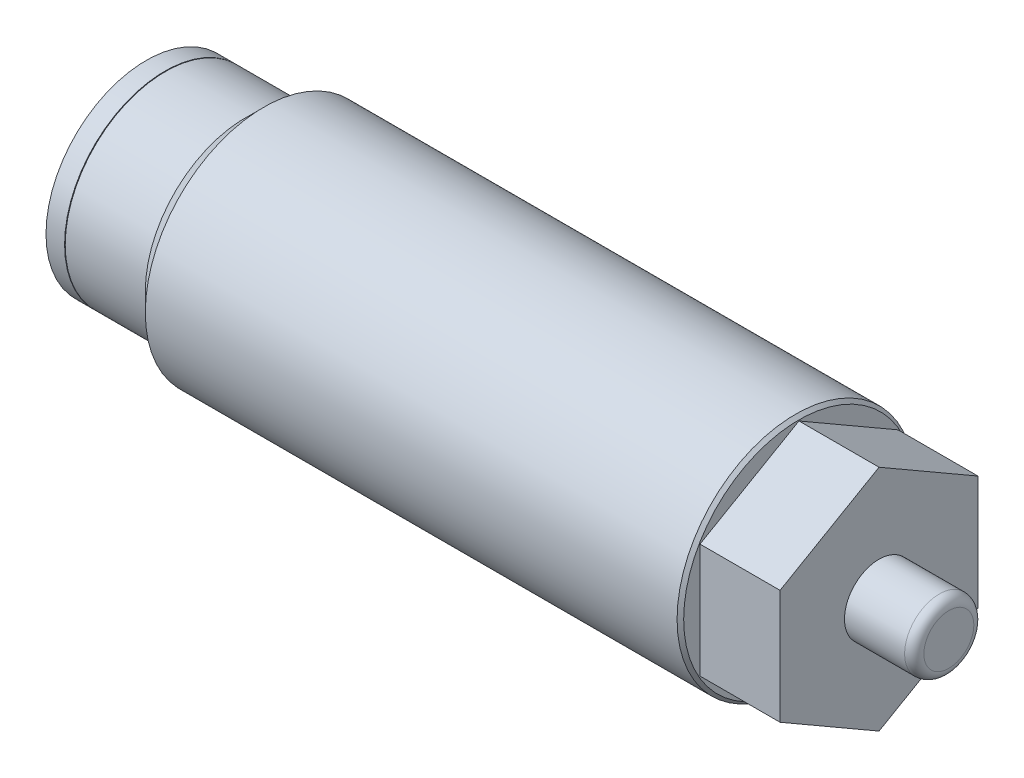
SolidWorks part; units mm, degrees
material "Alloy Steel"
ref_plane "Front Plane" through (0, 0, 0) normal (0, 0, 1) x (1, 0, 0)
ref_plane "Top Plane" through (0, 0, 0) normal (0, 1, 0) x (1, 0, 0)
ref_plane "Right Plane" through (0, 0, 0) normal (1, 0, 0) x (0, 0, -1)
sketch "Sketch11" plane through (0, 0, 0) normal (0, 0, 1) x (1, 0, 0)
  line L0 (-0.0254, 3.9751) -> (-0.762, 3.9751)
  line L1 (-0.762, 3.9751) -> (-0.762, 1.905)
  line L2 (-0.762, 1.905) -> (-0.0254, 1.905)
  line L3 (-0.0254, 1.905) -> (-0.0254, 3.9751)
  line L4 (-0.762, 0) -> (-0.0254, 0) construction
  dimension "D1" = 3.81
  dimension "D2" = 0.7366
  dimension "D3" = 7.9502
  dimension "D4" = 0.0254
revolve "Revolve5" add sketch "Sketch11" angle 360 about L4
ref_plane "Plane4" through (0, 0, 0) normal (0, 0, -1) x (-1, 0, 0)
sketch "Sketch12" plane through (0, 0, 0) normal (0, 0, -1) x (-1, 0, 0)
  line L0 (-25.1206, 4.7028) -> (-25.1206, 0)
  line L1 (0.0254, 3.9751) -> (0.0254, -3.9751) construction
  line L2 (0, 0) -> (0, 3.9751)
  line L3 (0, 3.9751) -> (-3.175, 3.9751)
  line L4 (-3.175, 3.9751) -> (-3.9027, 4.7028)
  line L5 (-3.9027, 4.7028) -> (-25.1206, 4.7028)
  line L6 (-30.6025, 0) -> (0, 0) construction
  line L7 (-25.1206, 0) -> (0, 0)
  dimension "D1" = 9.4056
  dimension "D2" = 0.0254
  dimension "D3" = 7.9502
  dimension "D4" = 45
  dimension "D5" = 3.175
  dimension "D6" = 25.1206
revolve "Revolve6" add sketch "Sketch12" angle 360 about L6
sketch "Sketch13" plane through (25.1206, 0, 0) normal (1, 0, 0) x (0, 0, -1)
  line L7 (3.9243, 2.2657) -> (0, 4.5314)
  line L8 (0, 4.5314) -> (-3.9243, 2.2657)
  line L9 (-3.9243, 2.2657) -> (-3.9243, -2.2657)
  line L10 (-3.9243, -2.2657) -> (0, -4.5314)
  line L11 (0, -4.5314) -> (3.9243, -2.2657)
  line L12 (3.9243, -2.2657) -> (3.9243, 2.2657)
  circle A0 centre (0, 0) radius 3.9243 construction
  dimension "D1" = 7.8486
extrude "Extrude3" add sketch "Sketch13" along normal blind 3.175
ref_plane "Plane5" through (0, 0, 0) normal (0, 0, 1) x (1, 0, 0)
sketch "Sketch14" plane through (0, 0, 0) normal (0, 0, 1) x (1, 0, 0)
  line L0 (28.2956, 1.3716) -> (28.2956, 0)
  line L1 (28.2956, 2.2657) -> (28.2956, -2.2657) construction
  line L2 (31.0642, 0) -> (31.0642, 1.3716)
  line L3 (31.0642, 1.3716) -> (28.2956, 1.3716)
  line L4 (28.2956, 0) -> (32.4342, 0) construction
  line L5 (28.2956, 0) -> (31.0642, 0)
  dimension "D1" = 2.7432
  dimension "D2" = 31.0642
revolve "Revolve7" add sketch "Sketch14" angle 360 about L4
hole_wizard "Hole3" positions "Sketch16" profile "Sketch15" legacy
sketch "Sketch16" plane through (0, 0, 0) normal (-1, 0, 0) x (0, 0, 1)
  point P0 (0, 0)
sketch "Sketch15" plane through (0, 0, 0) normal (0, 1, 0) x (0, 0, 1)
  line L0 (0, 0) -> (0, 0.254)
  line L1 (0, 0.254) -> (2.4892, 0.254)
  line L2 (2.4892, 0.254) -> (2.4892, 0)
  line L3 (2.4892, 0) -> (0, 0)
  line L4 (0, 110) -> (0, -10) construction
  dimension "Diameter" = 4.9784
  dimension "Depth" = 0.254
chamfer "Chamfer3" distance 0.1308 angle 45 1 edges at (25.1206, 0, 4.7028)
fillet "Fillet3" radius 0.381 1 edges at (31.0642, 0, -1.3716)
